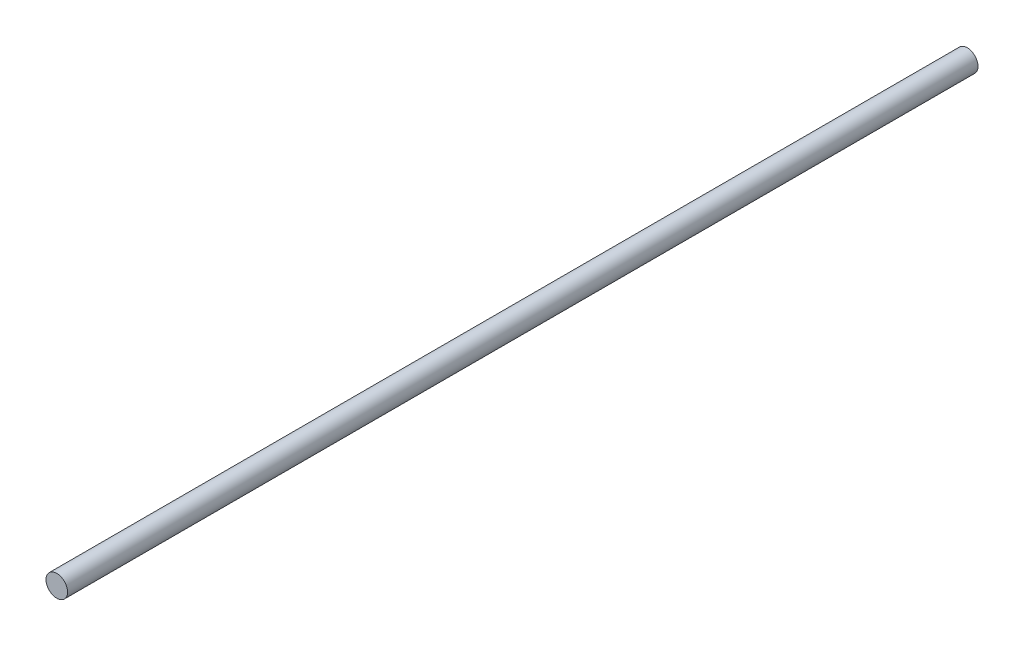
SolidWorks part; units mm, degrees
ref_plane "Front Plane" through (0, 0, 0) normal (0, 0, 1) x (1, 0, 0)
ref_plane "Top Plane" through (0, 0, 0) normal (0, 1, 0) x (1, 0, 0)
ref_plane "Right Plane" through (0, 0, 0) normal (1, 0, 0) x (0, 0, -1)
sketch "Sketch1" plane through (0, 0, 0) normal (0, 0, 1) x (1, 0, 0)
  circle A0 centre (0, 0) radius 6.35
  dimension "D1" = 12.7
extrude "Boss-Extrude2" add sketch "Sketch1" along normal mid plane 536
cosmetic thread "Cosmetic Thread1" parameters "D1"=44.5, "D2"=11.1887
cosmetic thread "Cosmetic Thread2" parameters "D1"=44.5, "D2"=11.1887
